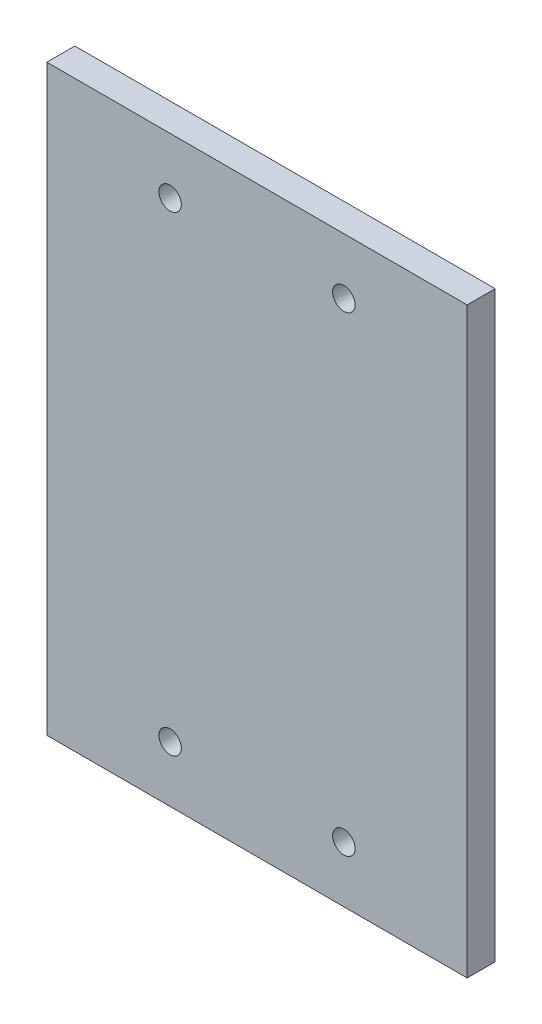
SolidWorks part; units mm, degrees
ref_plane "Front Plane" through (0, 0, 0) normal (0, 0, 1) x (1, 0, 0)
ref_plane "Top Plane" through (0, 0, 0) normal (0, 1, 0) x (1, 0, 0)
ref_plane "Right Plane" through (0, 0, 0) normal (1, 0, 0) x (0, 0, -1)
sketch "Sketch1" plane through (0, 0, 0) normal (0, 0, 1) x (1, 0, 0)
  line L0 (37.5, -52) -> (37.5, 52)
  line L1 (37.5, 52) -> (-37.5, 52)
  line L2 (-37.5, 52) -> (-37.5, -52)
  line L3 (-37.5, -52) -> (37.5, -52)
  circle A0 centre (15.5, -42) radius 2
  circle A1 centre (-15.5, -42) radius 2
  circle A2 centre (15.5, 42) radius 2
  circle A3 centre (-15.5, 42) radius 2
extrude "Boss-Extrude1" add sketch "Sketch1" along normal blind 5
